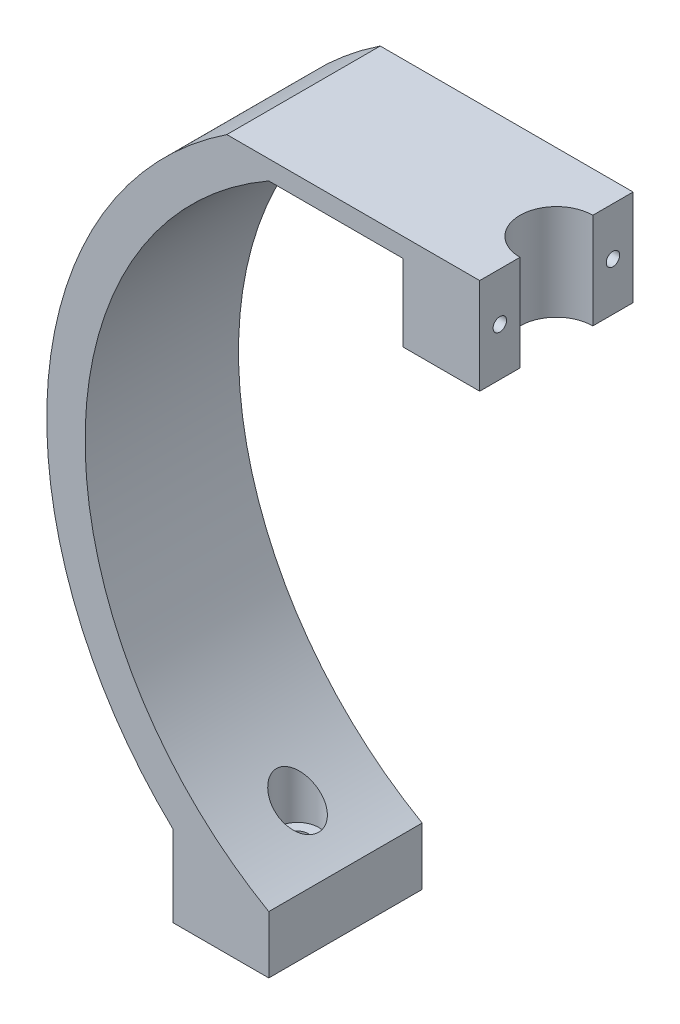
SolidWorks part; units mm, degrees
ref_plane "Front Plane" through (0, 0, 0) normal (0, 0, 1) x (1, 0, 0)
ref_plane "Top Plane" through (0, 0, 0) normal (0, 1, 0) x (1, 0, 0)
ref_plane "Right Plane" through (0, 0, 0) normal (1, 0, 0) x (0, 0, -1)
sketch "Sketch1" plane through (0, 0, 0) normal (0, 0, 1) x (1, 0, 0)
  line L0 (0, 0) -> (0, 185) construction
  line L1 (0, 97.5) -> (64.3645, 97.5) construction
  line L2 (0, 185) -> (-91.3019, 185) construction
  line L3 (0, 15) -> (0, 0)
  line L4 (0, 0) -> (-25, 0)
  line L5 (-25, 0) -> (-25, 21.1713)
  line L6 (-10.9373, 185) -> (55, 185)
  line L7 (55, 185) -> (55, 160)
  line L8 (55, 160) -> (35, 160)
  line L9 (35, 160) -> (35, 180)
  line L10 (35, 180) -> (0, 180)
  line L11 (-30, 0) -> (55, 0) construction
  arc A0 (-10.9373, 185) -> (-25, 21.1713) centre (47.1036, 97.5) ccw
  arc A1 (0, 180) -> (0, 15) centre (47.1036, 97.5) ccw
  point P3 (0, 180)
  point P4 (0, 15)
  dimension "D2" = 165
  dimension "D5" = 95
  dimension "D6" = 21.1713
  dimension "D8" = 105
  dimension "D1" = 185
  dimension "D3" = 5
  dimension "D4" = 82.5
  dimension "D7" = 25
  dimension "D9" = 85
  dimension "D10" = 5
  dimension "D11" = 0
  dimension "D12" = 20
  dimension "D13" = 25
extrude "Boss-Extrude1" add sketch "Sketch1" along normal blind 40 contours A1 L10 L9 L8 L7 L6 A0 L5 L4 L3
sketch "Sketch2" plane through (0, 185, 0) normal (0, 1, 0) x (1, 0, 0)
  line L0 (55, -40) -> (55, 0) construction
  circle A0 centre (55, -20) radius 9.5
  dimension "D1" = 19
extrude "Cut-Extrude1" cut sketch "Sketch2" against normal through all
sketch "Sketch3" plane through (0, 0, 0) normal (0, -1, 0) x (1, 0, 0)
  line L0 (0, 40) -> (0, 0) construction
  line L1 (0, 40) -> (-25, 40) construction
  circle A0 centre (-12.5, 20) radius 2.75
  dimension "D1" = 12.5
  dimension "D2" = 20
  dimension "D3" = 5.5
extrude "Cut-Extrude2" cut sketch "Sketch3" against normal blind 40
sketch "Sketch4" plane through (0, 0, 0) normal (0, -1, 0) x (1, 0, 0)
  circle A0 centre (-12.5, 20) radius 5.5
  dimension "D1" = 11
extrude "Cut-Extrude3" cut sketch "Sketch4" against normal blind 29 from offset 15 offset against normal yes
sketch "Sketch5" plane through (55, 0, 0) normal (1, 0, 0) x (0, 0, -1)
  line L0 (0, 185) -> (0, 160) construction
  circle A0 centre (-5.25, 172.5) radius 1.75
  circle A1 centre (-34.75, 172.5) radius 1.75
  dimension "D1" = 3.5
  dimension "D2" = 5.25
  dimension "D3" = 3.5
extrude "Cut-Extrude4" cut sketch "Sketch5" against normal blind 31
